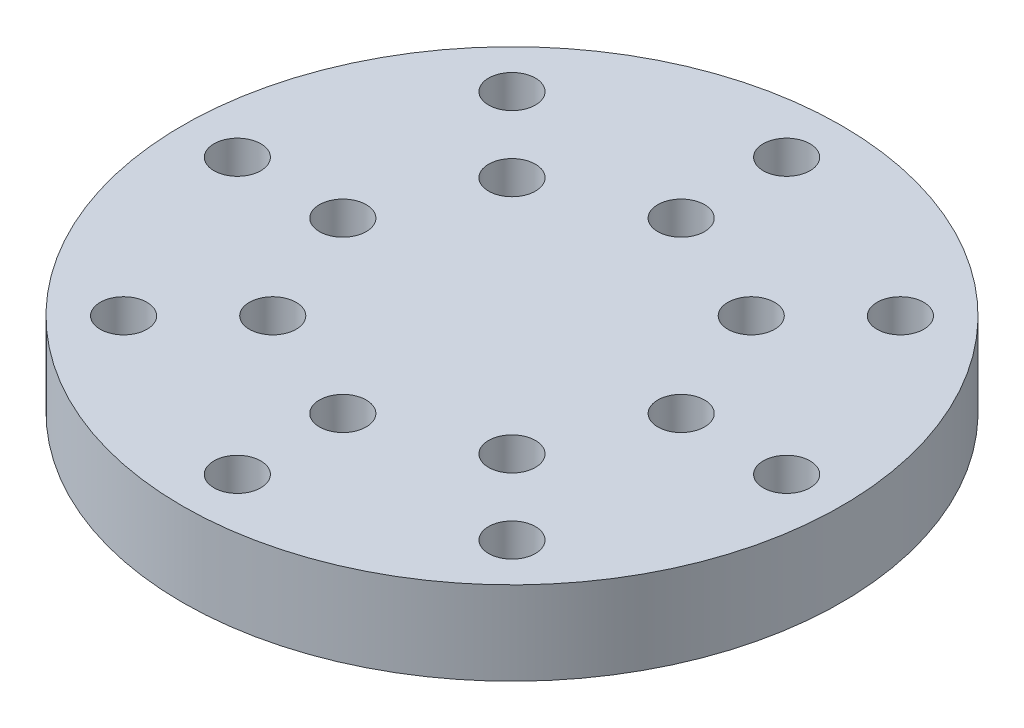
SolidWorks part; units mm, degrees
ref_plane "Front Plane" through (0, 0, 0) normal (0, 0, 1) x (1, 0, 0)
ref_plane "Top Plane" through (0, 0, 0) normal (0, 1, 0) x (1, 0, 0)
ref_plane "Right Plane" through (0, 0, 0) normal (1, 0, 0) x (0, 0, -1)
sketch "Sketch1" plane through (0, 0, 0) normal (0, 1, 0) x (1, 0, 0)
  line L0 (0, 19.05) -> (0, -19.05) construction
  line L1 (-19.05, 0) -> (19.05, 0) construction
  circle A0 centre (0, 0) radius 19.05
  circle A1 centre (0, 0) radius 15.875 construction
  circle A2 centre (0, 0) radius 9.779 construction
  point P9 (0, 15.875)
  point P10 (0, 9.779)
  dimension "D1" = 38.1
  dimension "D2" = 31.75
  dimension "D3" = 19.558
extrude "Boss-Extrude1" add sketch "Sketch1" along normal blind 4.826
hole_wizard "M2.5 Clearance Hole2" positions "Sketch10" profile "Sketch11" hole size "M2.5" standard "ANSI Metric"
sketch "Sketch10" plane through (0, 0, 0) normal (0, -1, 0) x (-1, 0, 0)
  point P0 (0, 15.875)
  point P3 (0, 9.779)
sketch "Sketch11" plane through (0, 0, -15.875) normal (1, 0, 0) x (0, 0, -1)
  line L0 (0, 0) -> (0, 5.8927)
  line L1 (0, 5.8927) -> (1.3525, 5.08)
  line L2 (1.3525, 5.08) -> (1.3525, 0)
  line L5 (1.3525, 0) -> (0, 0)
  line L10 (0, 5.8927) -> (-1.3525, 5.08) construction
  line L11 (0, -6.35) -> (0, 107.95) construction
  dimension "Hole Dia." = 2.7051
  dimension "Hole Depth" = 5.08
  dimension "Drill Angle" = 118
pattern_circular "CirPattern1" count 8 over 360 about axis through (0, 0, 0) along (0, 1, 0) of "M2.5 Clearance Hole2"
